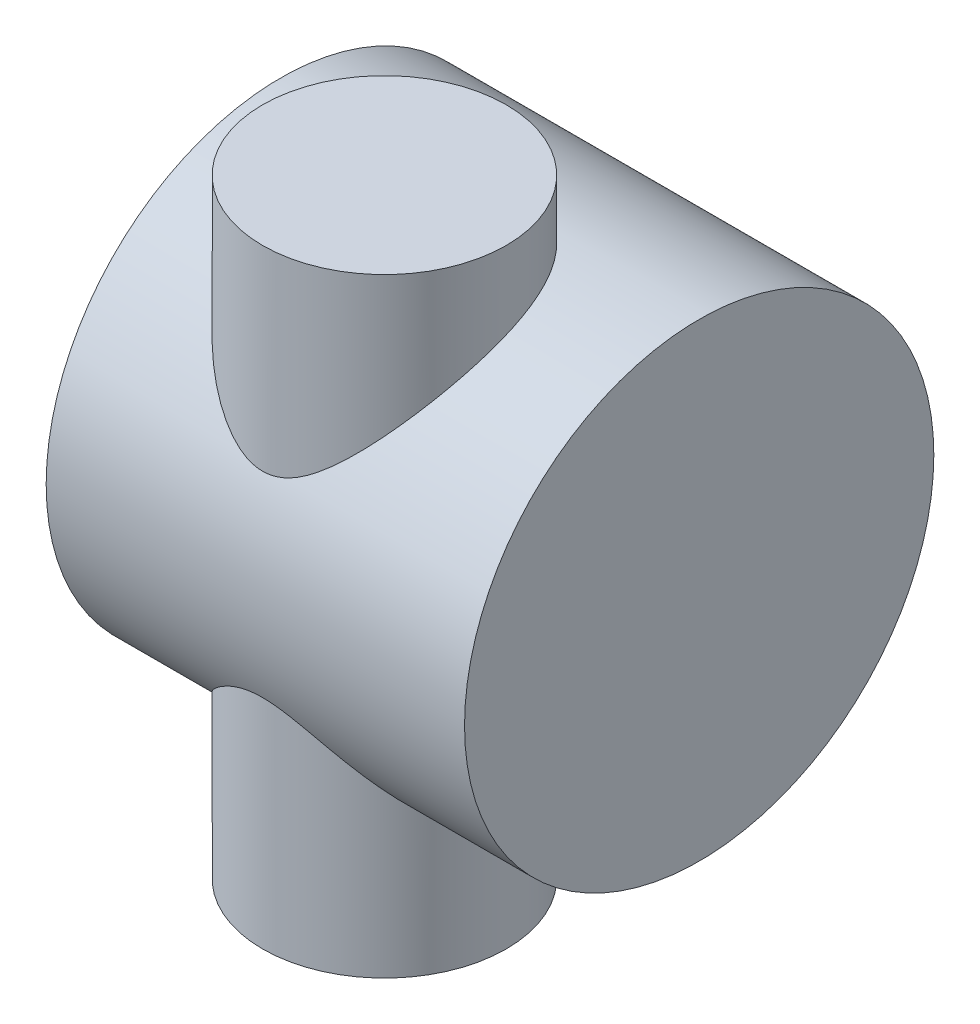
SolidWorks part; units mm, degrees
ref_plane "Front Plane" through (0, 0, 0) normal (0, 0, 1) x (1, 0, 0)
ref_plane "Top Plane" through (0, 0, 0) normal (0, 1, 0) x (1, 0, 0)
ref_plane "Right Plane" through (0, 0, 0) normal (1, 0, 0) x (0, 0, -1)
sketch "Sketch1" plane through (0, 0, 0) normal (0, 1, 0) x (1, 0, 0)
  circle A0 centre (0, 0) radius 30
extrude "Boss-Extrude1" add sketch "Sketch1" along normal blind 150
ref_plane "Plane1" through (30, 0, 0) normal (1, 0, 0) x (0, 0, -1)
sketch "Sketch3" plane through (30, 0, 0) normal (1, 0, 0) x (0, 0, -1)
  circle A1 centre (22.4942, 77.7316) radius 57.7697
extrude "Boss-Extrude2" add sketch "Sketch3" along normal blind 25 and the other way blind 78 contours A1
